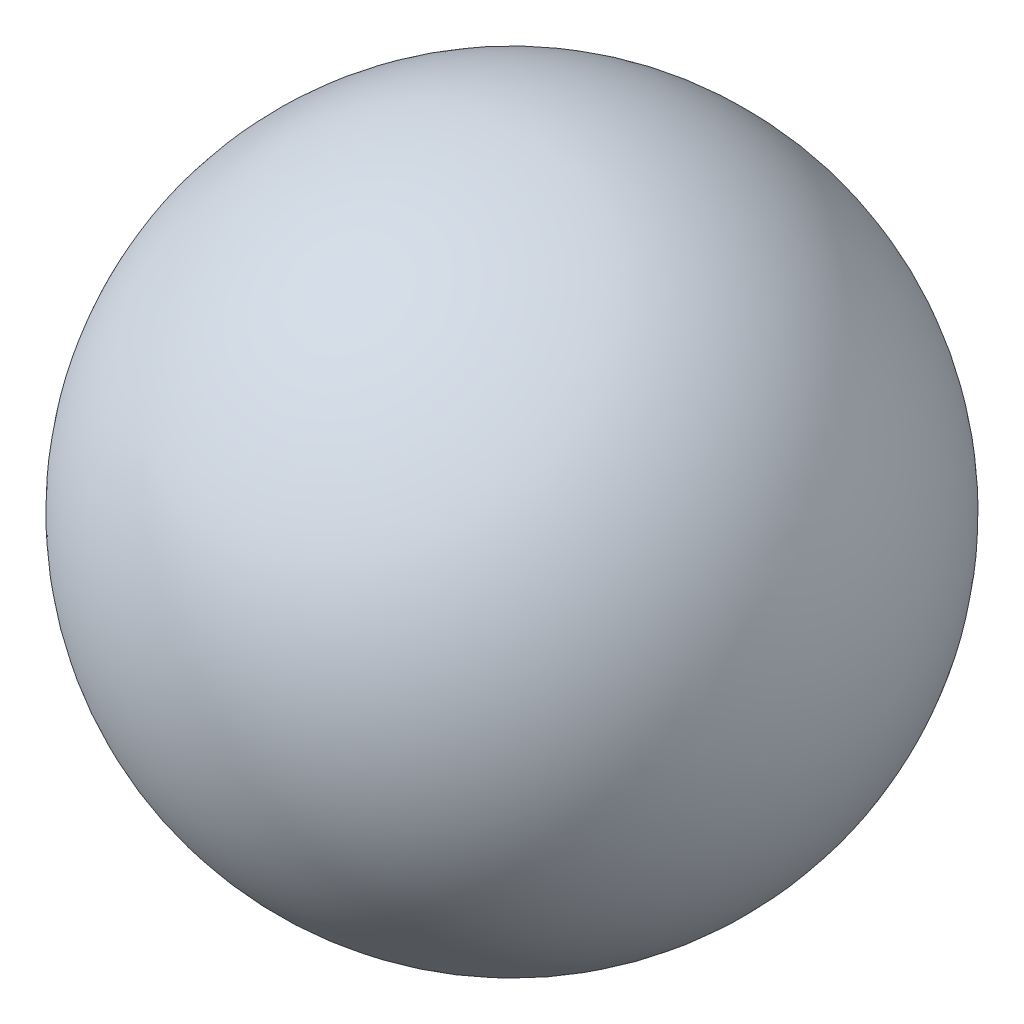
SolidWorks part; units mm, degrees
material "lead"
ref_plane "Front Plane" through (0, 0, 0) normal (0, 0, 1) x (1, 0, 0)
ref_plane "Top Plane" through (0, 0, 0) normal (0, 1, 0) x (1, 0, 0)
ref_plane "Right Plane" through (0, 0, 0) normal (1, 0, 0) x (0, 0, -1)
sketch "Sketch1" plane through (0, 0, 0) normal (0, 0, 1) x (1, 0, 0)
  line L0 (0, 0) -> (2.2829, 0) construction
  line L1 (1.651, 0) -> (-1.651, 0)
  arc A0 (1.651, 0) -> (-1.651, 0) centre (0, 0) ccw
  dimension "D1" = 3.302
revolve "Revolve2" add sketch "Sketch1" angle 360 about L0
